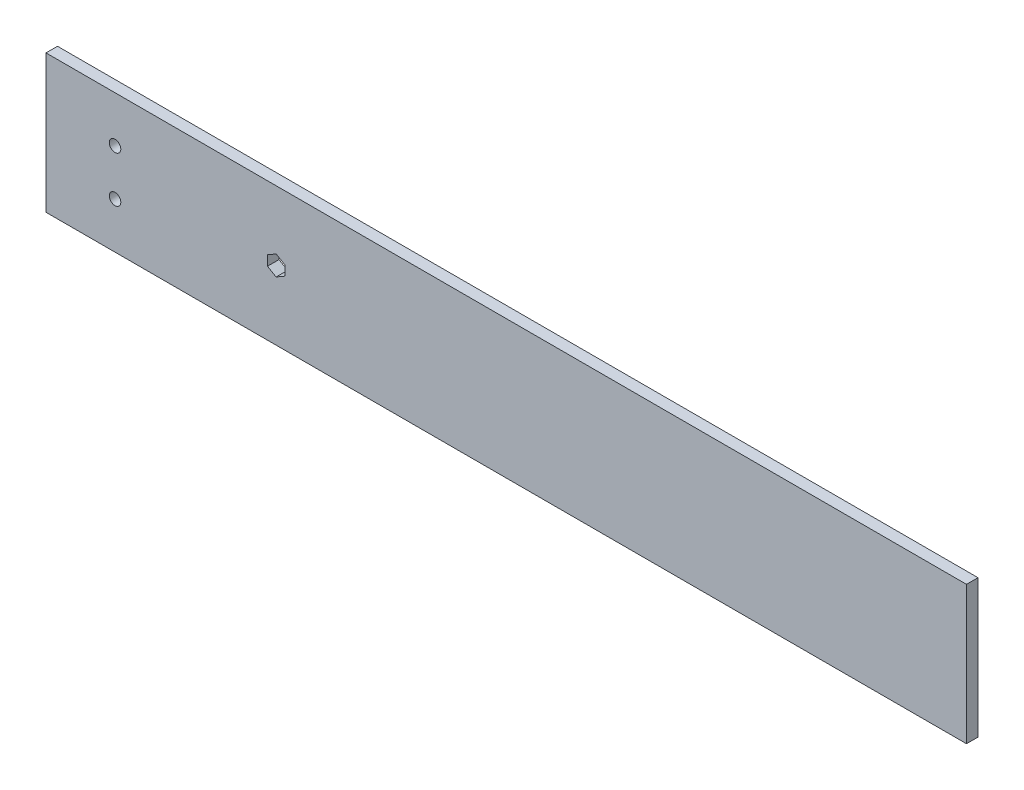
SolidWorks part; units mm, degrees
ref_plane "Front" through (0, 0, 0) normal (0, 0, 1) x (1, 0, 0)
ref_plane "Top" through (0, 0, 0) normal (0, 1, 0) x (1, 0, 0)
ref_plane "Right" through (0, 0, 0) normal (1, 0, 0) x (0, 0, -1)
sketch "Sketch1" plane through (0, 0, 0) normal (0, 0, 1) x (1, 0, 0)
  line L1 (0, 0) -> (508, 0)
  line L2 (0, 0) -> (0, 76.2)
  line L3 (0, 76.2) -> (508, 76.2)
  line L4 (508, 0) -> (508, 76.2)
  dimension "D1" = 508
  dimension "D2" = 76.2
extrude "Boss-Extrude1" add sketch "Sketch1" along normal blind 6.35
sketch "Sketch4" plane through (0, 0, 6.35) normal (0, 0, 1) x (1, 0, 0)
  line L0 (127, 76.2) -> (127, 0)
  line L1 (508, 76.2) -> (0, 76.2) construction
  line L2 (0, 0) -> (508, 0) construction
  line L3 (0, 76.2) -> (0, 0) construction
  line L5 (127, 43.5991) -> (122.2376, 40.8495)
  line L6 (122.2376, 40.8495) -> (122.2376, 35.3504)
  line L7 (122.2376, 35.3504) -> (127, 32.6009)
  line L8 (127, 32.6009) -> (131.7624, 35.3504)
  line L9 (131.7624, 35.3504) -> (131.7624, 40.8495)
  line L10 (131.7624, 40.8495) -> (127, 43.5991)
  circle A0 centre (127, 38.1) radius 4.7624 construction
  dimension "D1" = 127
  dimension "D2" = 10.9982
  dimension "D3" = 9.5247
extrude "Cut-Extrude6" cut sketch "Sketch4" against normal through all contours L5 L6 L7 L8 L9 L10
sketch "Sketch6" plane through (0, 0, 6.35) normal (0, 0, 1) x (1, 0, 0)
  line L0 (0, 76.2) -> (0, 0) construction
  line L1 (508, 76.2) -> (0, 76.2) construction
  line L2 (0, 38.1) -> (56.7409, 38.1) construction
  circle A0 centre (38.1, 50.8) radius 3.175
  circle A1 centre (38.1, 25.4) radius 3.175
  dimension "D3" = 6.35
  dimension "D1" = 38.1
  dimension "D2" = 25.4
extrude "Cut-Extrude7" cut sketch "Sketch6" against normal through all
